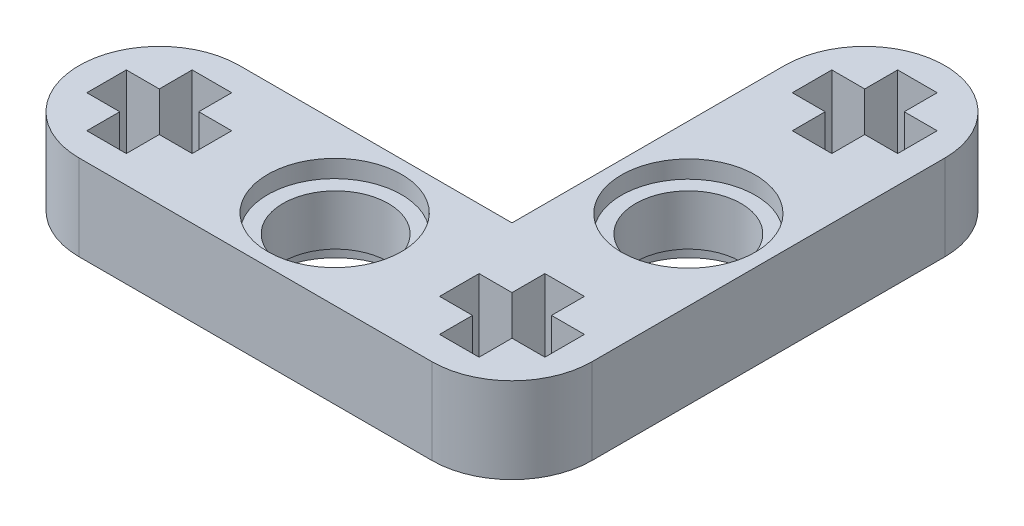
SolidWorks part; units mm, degrees
ref_plane "Front Plane" through (0, 0, 0) normal (0, 0, 1) x (1, 0, 0)
ref_plane "Top Plane" through (0, 0, 0) normal (0, 1, 0) x (1, 0, 0)
ref_plane "Right Plane" through (0, 0, 0) normal (1, 0, 0) x (0, 0, -1)
sketch "Sketch1" plane through (0, 0, 0) normal (0, 1, 0) x (1, 0, 0)
  line L0 (-7.9899, 0) -> (8.0801, 0) construction
  line L1 (-55, 0) -> (55, 0) construction
  line L2 (-7.9899, 3.65) -> (4.4301, 3.65)
  line L3 (-7.9899, -3.65) -> (8.0801, -3.65)
  line L4 (8.9801, 16.97) -> (10.4801, 16.97)
  line L7 (8.0801, 0) -> (8.0801, 16.07) construction
  line L10 (4.4301, 3.65) -> (4.4301, 16.07)
  line L11 (11.7301, 0) -> (11.7301, 16.07)
  line L12 (-8.8899, -2.4) -> (-7.0899, -2.4)
  line L13 (-8.8899, -2.4) -> (-8.8899, -0.9)
  line L14 (-8.8899, 2.4) -> (-7.0899, 2.4)
  line L15 (-7.0899, -2.4) -> (-7.0899, -0.9)
  line L16 (-8.8899, -2.4) -> (-7.0899, 2.4) construction
  line L17 (-8.8899, 2.4) -> (-7.0899, -2.4) construction
  line L18 (-10.3899, -0.9) -> (-8.8899, -0.9)
  line L19 (-10.3899, -0.9) -> (-10.3899, 0.9)
  line L20 (-10.3899, 0.9) -> (-8.8899, 0.9)
  line L21 (-5.5899, -0.9) -> (-5.5899, 0.9)
  line L22 (-10.3899, -0.9) -> (-5.5899, 0.9) construction
  line L23 (-10.3899, 0.9) -> (-5.5899, -0.9) construction
  line L24 (7.1801, -2.4) -> (8.9801, -2.4)
  line L25 (7.1801, -2.4) -> (7.1801, -0.9)
  line L26 (7.1801, 2.4) -> (8.9801, 2.4)
  line L27 (8.9801, -2.4) -> (8.9801, -0.9)
  line L28 (7.1801, -2.4) -> (8.9801, 2.4) construction
  line L29 (7.1801, 2.4) -> (8.9801, -2.4) construction
  line L30 (5.6801, -0.9) -> (7.1801, -0.9)
  line L31 (5.6801, -0.9) -> (5.6801, 0.9)
  line L32 (5.6801, 0.9) -> (7.1801, 0.9)
  line L33 (10.4801, -0.9) -> (10.4801, 0.9)
  line L34 (5.6801, -0.9) -> (10.4801, 0.9) construction
  line L35 (5.6801, 0.9) -> (10.4801, -0.9) construction
  line L36 (7.1801, 18.47) -> (8.9801, 18.47)
  line L37 (7.1801, 18.47) -> (7.1801, 16.97)
  line L38 (7.1801, 13.67) -> (8.9801, 13.67)
  line L39 (8.9801, 18.47) -> (8.9801, 16.97)
  line L40 (7.1801, 18.47) -> (8.9801, 13.67) construction
  line L41 (7.1801, 13.67) -> (8.9801, 18.47) construction
  line L42 (5.6801, 16.97) -> (7.1801, 16.97)
  line L43 (5.6801, 16.97) -> (5.6801, 15.17)
  line L44 (5.6801, 15.17) -> (7.1801, 15.17)
  line L45 (10.4801, 16.97) -> (10.4801, 15.17)
  line L46 (5.6801, 16.97) -> (10.4801, 15.17) construction
  line L47 (5.6801, 15.17) -> (10.4801, 16.97) construction
  line L48 (7.1801, 15.17) -> (7.1801, 13.67)
  line L49 (8.9801, 15.17) -> (10.4801, 15.17)
  line L50 (8.9801, 15.17) -> (8.9801, 13.67)
  line L51 (8.9801, 0.9) -> (8.9801, 2.4)
  line L52 (8.9801, -0.9) -> (10.4801, -0.9)
  line L53 (7.1801, 0.9) -> (7.1801, 2.4)
  line L54 (8.9801, 0.9) -> (10.4801, 0.9)
  line L55 (-8.8899, 0.9) -> (-8.8899, 2.4)
  line L56 (-7.0899, -0.9) -> (-5.5899, -0.9)
  line L57 (-7.0899, 0.9) -> (-7.0899, 2.4)
  line L58 (-7.0899, 0.9) -> (-5.5899, 0.9)
  arc A0 (-7.9899, 3.65) -> (-7.9899, -3.65) centre (-7.9899, 0) ccw
  arc A1 (8.0801, -3.65) -> (11.7301, 0) centre (8.0801, 0) ccw
  arc A7 (11.7301, 16.07) -> (4.4301, 16.07) centre (8.0801, 16.07) ccw
  circle A8 centre (0.0451, 0) radius 2.4
  circle A9 centre (8.0801, 8.035) radius 2.4
  point P5 (0.0451, 0)
  point P17 (8.0801, 8.035)
  dimension "D5" = 8.035
  dimension "D1" = 7.3
  dimension "D2" = 23.37
  dimension "D3" = 3.65
  dimension "D4" = 16.07
  dimension "D6" = 8.035
  dimension "D7" = 8.035
  dimension "D8" = 8.035
extrude "Boss-Extrude1" add sketch "Sketch1" along normal blind 3.9
sketch "Sketch2" plane through (0, 3.9, 0) normal (0, 1, 0) x (1, 0, 0)
  circle A0 centre (0, 0) radius 3.05
  circle A1 centre (8.0801, 8.035) radius 3.05
extrude "Cut-Extrude1" cut sketch "Sketch2" against normal blind 0.8
sketch "Sketch3" plane through (0, 0, 0) normal (0, -1, 0) x (1, 0, 0)
  line L0 (8.0801, -5.635) -> (8.0801, -10.435) construction
  line L1 (8.0801, -10.435) -> (5.6801, -8.035) construction
  line L2 (5.6801, -8.035) -> (10.4801, -8.035) construction
  circle A0 centre (8.0801, -8.035) radius 2.4 construction
  circle A1 centre (8.0801, -8.035) radius 3.05
  circle A2 centre (0.0451, 0) radius 3.05
extrude "Cut-Extrude2" cut sketch "Sketch3" against normal blind 0.8
